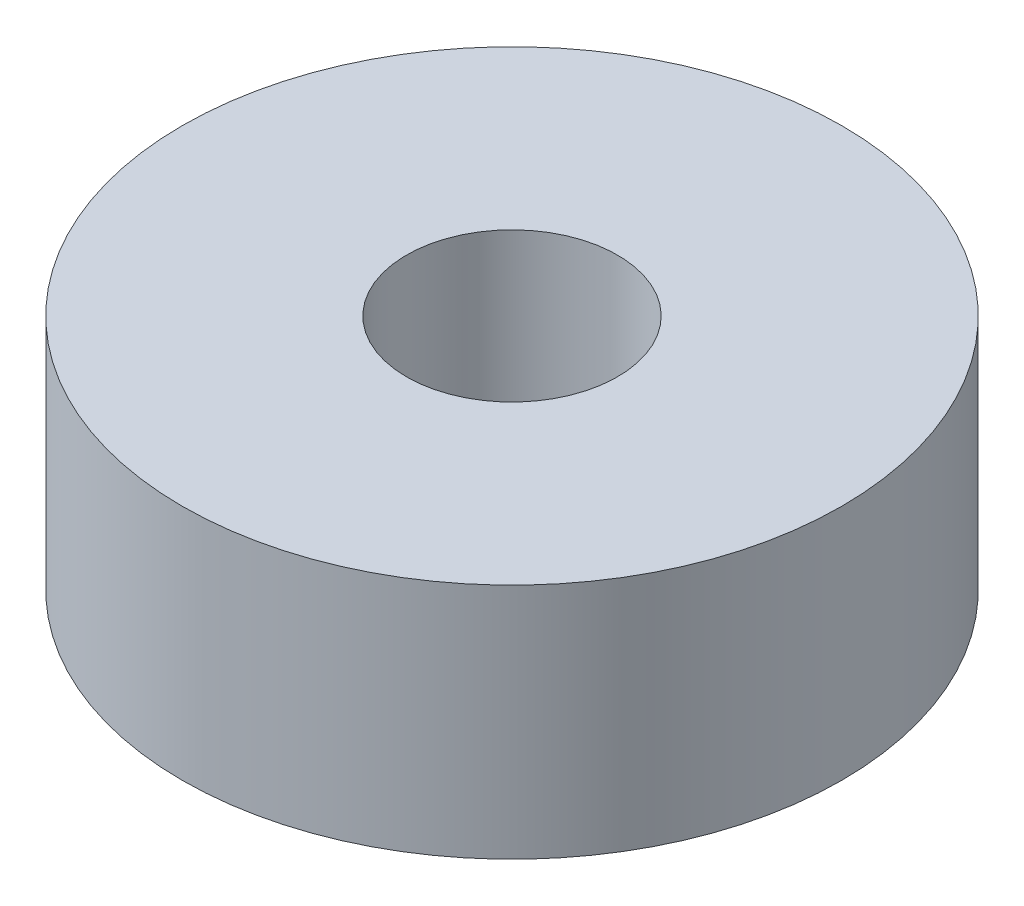
SolidWorks part; units mm, degrees
ref_plane "前视基准面" through (0, 0, 0) normal (0, 0, 1) x (1, 0, 0)
ref_plane "上视基准面" through (0, 0, 0) normal (0, 1, 0) x (1, 0, 0)
ref_plane "右视基准面" through (0, 0, 0) normal (1, 0, 0) x (0, 0, -1)
sketch "草图1" plane through (0, 0, 0) normal (0, 1, 0) x (1, 0, 0)
  circle A0 centre (0, 0) radius 8
  circle A1 centre (0, 0) radius 25
extrude "凸台-拉伸1" add sketch "草图1" along normal blind 18
